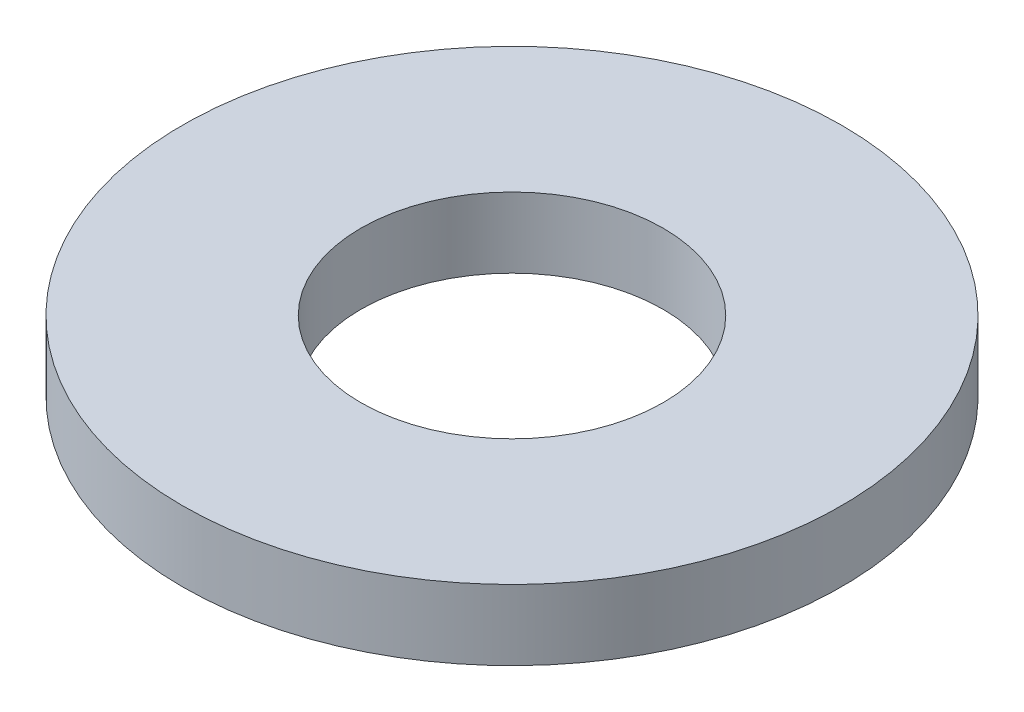
SolidWorks part; units mm, degrees
ref_plane "Front Plane" through (0, 0, 0) normal (0, 0, 1) x (1, 0, 0)
ref_plane "Top Plane" through (0, 0, 0) normal (0, 1, 0) x (1, 0, 0)
ref_plane "Right Plane" through (0, 0, 0) normal (1, 0, 0) x (0, 0, -1)
sketch "Sketch1" plane through (0, 0, 0) normal (0, 1, 0) x (1, 0, 0)
  circle A0 centre (0, 0) radius 4.7625
  dimension "OD" = 9.525
extrude "Boss-Extrude1" add sketch "Sketch1" along normal blind 1.016
sketch "Sketch5" plane through (0, 1.016, 0) normal (0, 1, 0) x (-1, 0, 0)
  circle A0 centre (0, 0) radius 2.1844
  dimension "ID" = 4.3688
extrude "Cut-Extrude1" cut sketch "Sketch5" against normal through all
